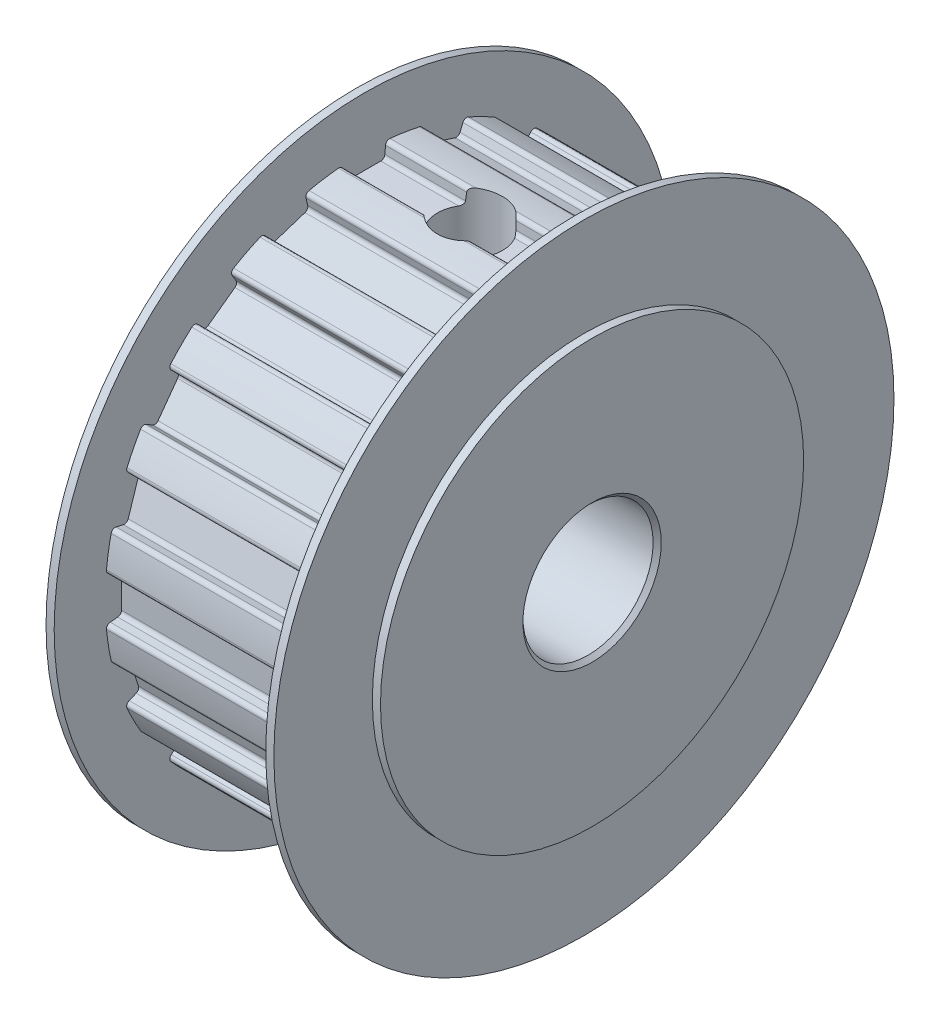
SolidWorks part; units mm, degrees
ref_plane "Plan de face" through (0, 0, 0) normal (0, 0, 1) x (1, 0, 0)
ref_plane "Plan de dessus" through (0, 0, 0) normal (0, 1, 0) x (1, 0, 0)
ref_plane "Plan de droite" through (0, 0, 0) normal (1, 0, 0) x (0, 0, -1)
sketch "Esquisse1" plane through (0, 0, 0) normal (1, 0, 0) x (0, 0, -1)
  circle A0 centre (0, 0) radius 15.915
  dimension "D1" = 31.83
extrude "Extrusion1" add sketch "Esquisse1" along normal blind 13
sketch "Esquisse22" plane through (0, 0, 0) normal (-1, 0, 0) x (0, 0, 1)
  line L0 (0, 0) -> (0, 15.915) construction
  line L1 (-1.25, 14.915) -> (1.25, 14.915)
  line L2 (0, 0) -> (1.25, 14.915) construction
  line L3 (0, 0) -> (-1.25, 14.915) construction
  line L4 (-1.25, 14.915) -> (-2.1271, 25.381)
  line L5 (1.25, 14.915) -> (2.1266, 25.3749)
  line L6 (-2.1271, 25.381) -> (2.1266, 25.3749)
  circle A0 centre (0, 0) radius 15.915 construction
  dimension "D1" = 2.5
  dimension "D2" = 1.25
  dimension "D3" = 1
  dimension "D4" = 180
  dimension "D5" = 180
extrude "Enlèv. mat.-Extru.2" cut sketch "Esquisse22" against normal up to next (13 mm away)
fillet "Congé1" radius 0.25 1 edges at (6.5, 14.915, -1.25)
fillet "Congé2" radius 0.25 1 edges at (6.5, 15.8594, -1.3291)
fillet "Congé3" radius 0.25 1 edges at (6.5, 14.915, 1.25)
fillet "Congé4" radius 0.25 1 edges at (6.5, 15.8594, 1.3291)
pattern_circular "Répétition circulaire1" count 20 over 360 about axis through (0, 0, 0) along (1, 0, 0) of "Enlèv. mat.-Extru.2", "Congé1", "Congé2", "Congé3", "Congé4"
sketch "Esquisse23" plane through (0, 0, 0) normal (-1, 0, 0) x (0, 0, 1)
  circle A0 centre (0, 0) radius 19.05
  dimension "D1" = 38.1
extrude "Extrusion2" add sketch "Esquisse23" along normal blind 1
sketch "Esquisse24" plane through (13, 0, 0) normal (1, 0, 0) x (0, 0, -1)
  circle A0 centre (0, 0) radius 19.05
  dimension "D1" = 38.1
extrude "Extrusion3" add sketch "Esquisse24" along normal blind 1
sketch "Esquisse25" plane through (-1, 0, 0) normal (-1, 0, 0) x (0, 0, 1)
  circle A0 centre (0, 0) radius 4
  dimension "D1" = 8
extrude "Enlèv. mat.-Extru.3" cut sketch "Esquisse25" against normal through all
sketch "Esquisse30" plane through (0, 14.915, 0) normal (0, 1, 0) x (-1, 0, 0)
  line L1 (-13, 0) -> (0, 0) construction
  line L3 (0, -1.0201) -> (0, 1.0201) construction
  circle A0 centre (-6.5, 0) radius 2
  dimension "D2" = 4
  dimension "D1" = 6.5
extrude "Enlèv. mat.-Extru.5" cut sketch "Esquisse30" against normal up to next and the other way through all
sketch "Esquisse31" plane through (-1, 0, 0) normal (-1, 0, 0) x (0, 0, 1)
  circle A0 centre (0, 0) radius 13
  dimension "D1" = 26
extrude "Enlèv. mat.-Extru.6" cut sketch "Esquisse31" against normal blind 0.5 flip side to cut
sketch "Esquisse32" plane through (14, 0, 0) normal (1, 0, 0) x (0, 0, -1)
  circle A0 centre (0, 0) radius 13
  dimension "D1" = 26
extrude "Enlèv. mat.-Extru.7" cut sketch "Esquisse32" against normal blind 0.5 flip side to cut
chamfer "Chanfrein1" distance 0.25 angle 45 1 edges at (14, 0, 4)
chamfer "Chanfrein2" distance 0.25 angle 45 1 edges at (-1, 0, 4)
